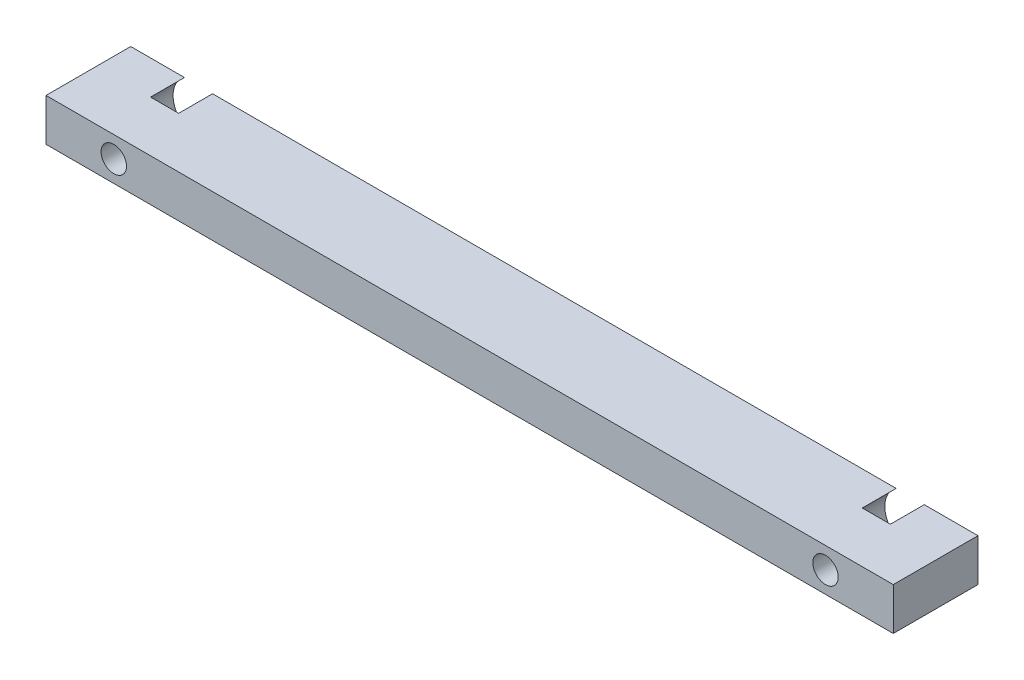
SolidWorks part; units mm, degrees
ref_plane "Front Plane" through (0, 0, 0) normal (0, 0, 1) x (1, 0, 0)
ref_plane "Top Plane" through (0, 0, 0) normal (0, 1, 0) x (1, 0, 0)
ref_plane "Right Plane" through (0, 0, 0) normal (1, 0, 0) x (0, 0, -1)
sketch "Sketch1" plane through (0, 0, 0) normal (0, 0, 1) x (1, 0, 0)
  line L1 (50, 2.5) -> (-50, 2.5)
  line L2 (50, 2.5) -> (50, -2.5)
  line L3 (50, -2.5) -> (-50, -2.5)
  line L4 (-50, 2.5) -> (-50, -2.5)
  line L5 (50, 2.5) -> (-50, -2.5) construction
  line L6 (50, -2.5) -> (-50, 2.5) construction
  point P0 (0, 0)
  dimension "D1" = 5
  dimension "D2" = 100
extrude "Boss-Extrude1" add sketch "Sketch1" along normal blind 10
sketch "Sketch2" plane through (0, 0, 0) normal (0, 0, -1) x (-1, 0, 0)
  line L0 (0, 2.75) -> (0, -2.75) construction
  line L1 (-50, -2.5) -> (-50, 2.5) construction
  circle A0 centre (-42, 0) radius 3
  circle A1 centre (42, 0) radius 3
  point P8 (0, 0)
  point P9 (0, 0)
  dimension "D1" = 6
  dimension "D2" = 8
extrude "Cut-Extrude3" cut sketch "Sketch2" against normal blind 4
sketch "Sketch3" plane through (0, 0, 4) normal (0, 0, -1) x (-1, 0, 0)
  line L0 (0, 2.75) -> (0, -2.75) construction
  circle A0 centre (-42, 0) radius 1.5
  arc A1 (-40.3417, -2.5) -> (-40.3417, 2.5) centre (-42, 0) ccw construction
  circle A2 centre (42, 0) radius 1.5
  dimension "D1" = 3
extrude "Cut-Extrude4" cut sketch "Sketch3" against normal through all
